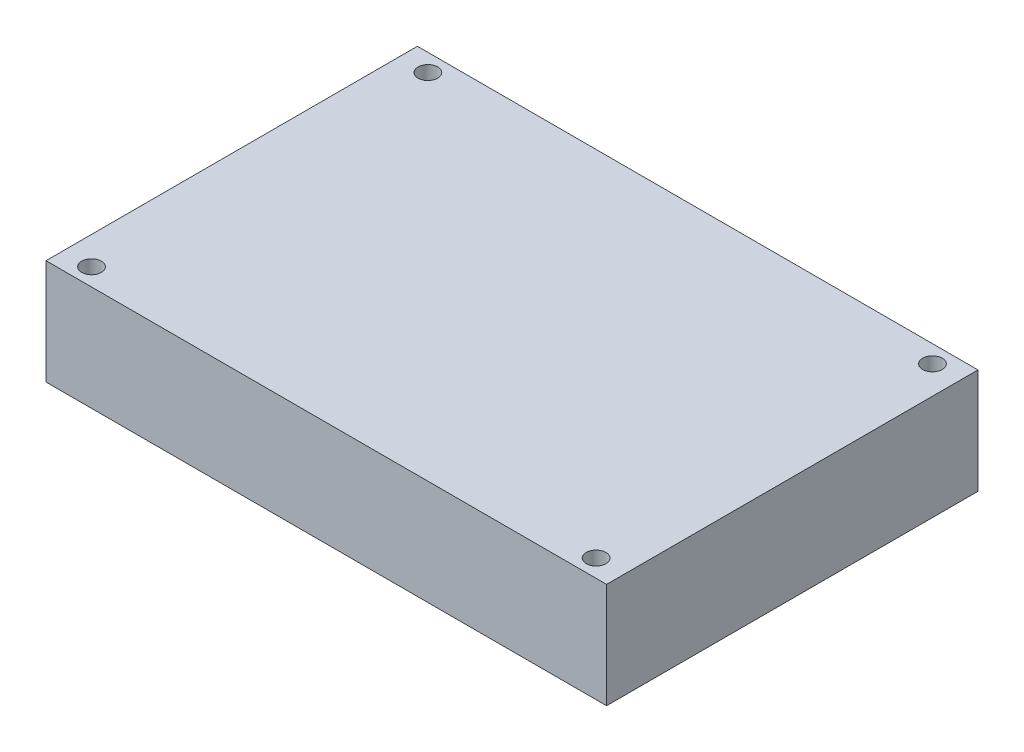
SolidWorks part; units mm, degrees
ref_plane "前视基准面" through (0, 0, 0) normal (0, 0, 1) x (1, 0, 0)
ref_plane "上视基准面" through (0, 0, 0) normal (0, 1, 0) x (1, 0, 0)
ref_plane "右视基准面" through (0, 0, 0) normal (1, 0, 0) x (0, 0, -1)
sketch "草图1" plane through (0, 0, 0) normal (0, 1, 0) x (1, 0, 0)
  line L0 (80, 53) -> (80, 0)
  line L1 (0, 0) -> (0, 53)
  line L2 (0, 53) -> (39.5, 53)
  line L3 (41.5, 53) -> (80, 53)
  line L4 (0, 0) -> (80, 0)
  line L5 (39.5, 53) -> (41.5, 53)
  circle A0 centre (76, 50.5) radius 1.4
  circle A1 centre (76, 2.5) radius 1.4
  circle A2 centre (4, 50.5) radius 1.4
  circle A3 centre (4, 2.5) radius 1.4
extrude "凸台-拉伸1" add sketch "草图1" along normal blind 15
